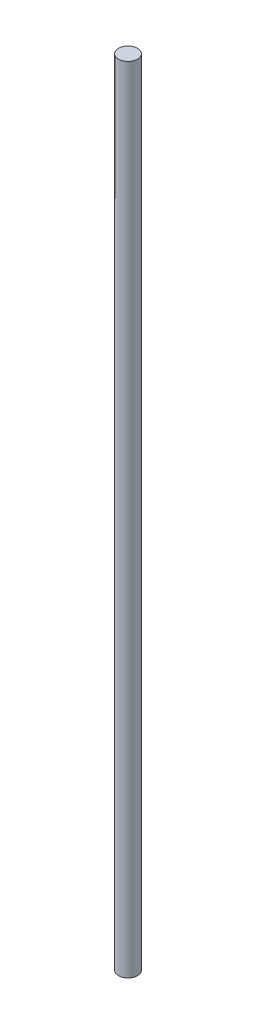
SolidWorks part; units mm, degrees
ref_plane "Front Plane" through (0, 0, 0) normal (0, 0, 1) x (1, 0, 0)
ref_plane "Top Plane" through (0, 0, 0) normal (0, 1, 0) x (1, 0, 0)
ref_plane "Right Plane" through (0, 0, 0) normal (1, 0, 0) x (0, 0, -1)
sketch "Sketch1" plane through (0, 0, 0) normal (0, 1, 0) x (1, 0, 0)
  circle A0 centre (0, 0) radius 2.555
  dimension "D2" = 5.11
extrude "Boss-Extrude1" add sketch "Sketch1" along normal blind 214 contours A0
cosmetic thread "Cosmetic Thread1" parameters "D2"=3.8811
